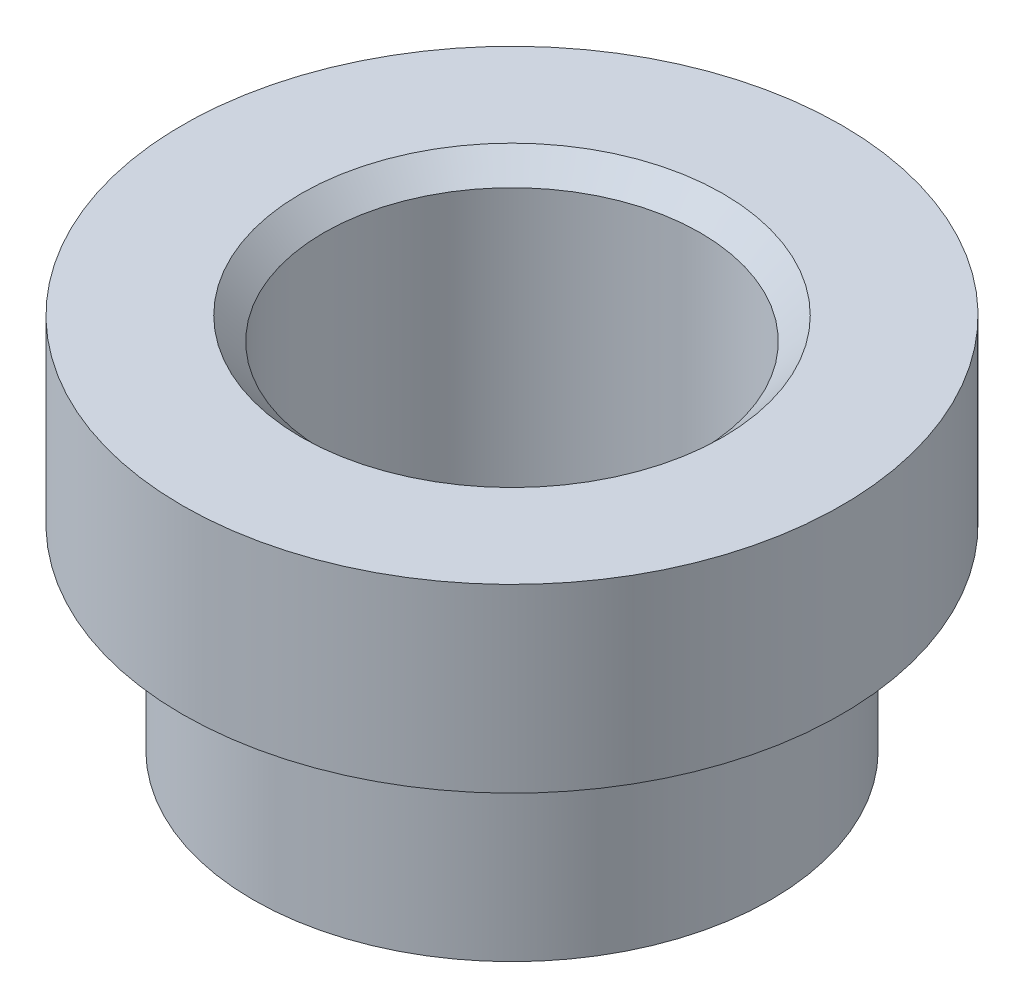
SolidWorks part; units mm, degrees
material "Delrin 2700 NC010, Low Viscosity Acetal Copolymer (SS)"
ref_plane "Front Plane" through (0, 0, 0) normal (0, 0, 1) x (1, 0, 0)
ref_plane "Top Plane" through (0, 0, 0) normal (0, 1, 0) x (1, 0, 0)
ref_plane "Right Plane" through (0, 0, 0) normal (1, 0, 0) x (0, 0, -1)
sketch "Sketch1" plane through (0, 0, 0) normal (0, 0, 1) x (1, 0, 0)
  line L0 (8.7313, 0) -> (11.1125, 0)
  line L1 (11.1125, 0) -> (11.1125, 6.096)
  line L2 (11.1125, 6.096) -> (6.35, 6.096)
  line L3 (6.35, 6.096) -> (6.35, -6.604)
  line L6 (6.35, -6.604) -> (8.7313, -6.604)
  line L7 (8.7313, -6.604) -> (8.7313, 0)
  line L8 (0, 0) -> (0, -6.604) construction
  dimension "D1" = 6.35
  dimension "D2" = 2.3813
  dimension "D3" = 11.1125
  dimension "D4" = 6.096
  dimension "D5" = 12.7
revolve "Revolve1" add sketch "Sketch1" angle 360 about L8
chamfer "Chamfer1" distance 0.762 angle 45 1 edges at (0, 6.096, 6.35)
